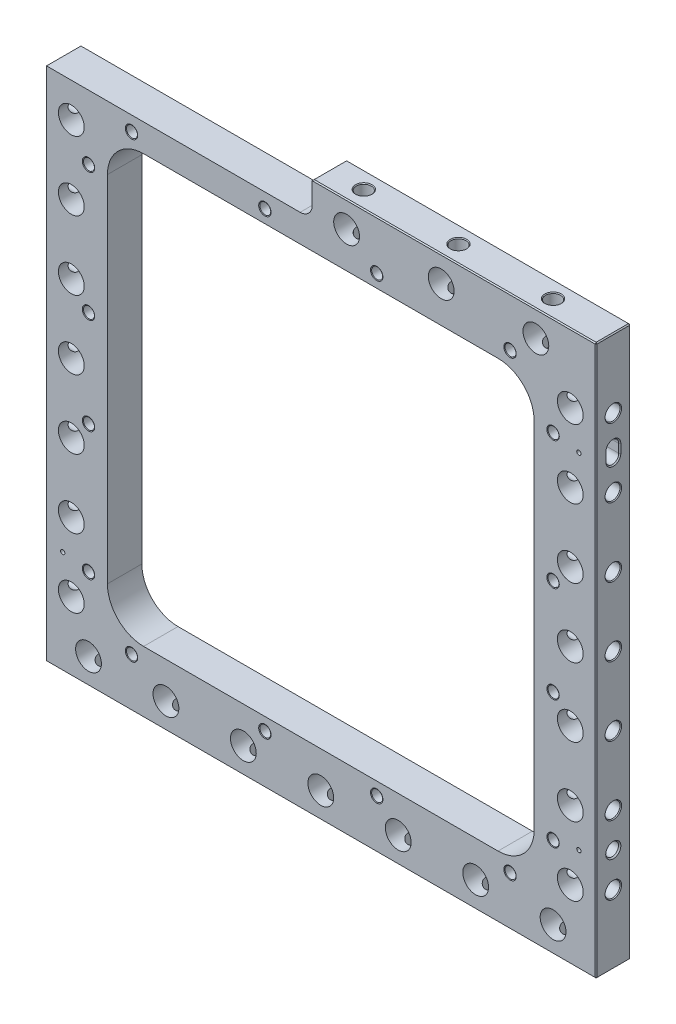
SolidWorks part; units mm, degrees
material "6061-T6 Al"
ref_plane "Front Plane" through (0, 0, 0) normal (0, 0, 1) x (1, 0, 0)
ref_plane "Top Plane" through (0, 0, 0) normal (0, 1, 0) x (1, 0, 0)
ref_plane "Right Plane" through (0, 0, 0) normal (1, 0, 0) x (0, 0, -1)
sketch "Sketch1" plane through (0, 0, 0) normal (0, 0, 1) x (1, 0, 0)
  line L0 (-203.2, 177.8) -> (-203.2, -203.2)
  line L1 (-203.2, -203.2) -> (203.2, -203.2)
  line L2 (203.2, -203.2) -> (203.2, 203.2)
  line L3 (203.2, 203.2) -> (-6.35, 203.2)
  line L4 (-6.35, 203.2) -> (-6.35, 177.8)
  line L5 (-6.35, 177.8) -> (-203.2, 177.8)
  line L6 (-203.2, -203.2) -> (203.2, 203.2) construction
  point P2 (0, 0)
  dimension "D1" = 406.4
  dimension "D2" = 209.55
  dimension "D3" = 406.4
  dimension "D4" = 25.4
extrude "Extrude1" add sketch "Sketch1" along normal mid plane 25.4
hole_wizard "3/4 (0.75) Diameter Hole1" positions "Sketch4" profile "Sketch3" hole size "3/4" standard "Ansi Inch" end condition through all
sketch "Sketch4" plane through (0, 0, 12.7) normal (0, 0, 1) x (1, 0, 0)
  line L0 (203.2, 0) -> (184.15, 0) construction
  line L1 (203.2, -203.2) -> (203.2, 203.2) construction
  line L5 (184.15, 0) -> (-184.15, 0) construction
  line L6 (-184.15, 0) -> (-203.2, 0) construction
  line L7 (-203.2, 177.8) -> (-203.2, -203.2) construction
  point P0 (184.15, 0)
  point P22 (-184.15, 0)
  dimension "D1" = 19.05
sketch "Sketch3" plane through (184.15, 0, 12.7) normal (1, 0, 0) x (0, -1, 0)
  line L0 (0, 0) -> (0, 25.4)
  line L1 (0, 25.4) -> (9.525, 25.4)
  line L2 (9.525, 25.4) -> (9.525, 0)
  line L5 (9.525, 0) -> (0, 0)
  line L11 (0, -6.35) -> (0, 107.95) construction
  dimension "Thru Hole Dia." = 19.05
  dimension "Thru Hole Depth" = 25.4
hole_wizard "7/16 (0.4375) Diameter Hole1" positions "Sketch6" profile "Sketch5" hole size "7/16" standard "Ansi Inch"
sketch "Sketch6" plane through (203.2, 0, 0) normal (1, 0, 0) x (0, 0, -1)
  line L0 (-12.7, 9.525) -> (-12.7, -9.525) construction
  line L1 (-12.7, 9.525) -> (-12.7, -9.525)
  line L2 (-12.7, 0) -> (0, 0) construction
  line L4 (0, 0) -> (12.7, 0) construction
  line L5 (12.7, -203.2) -> (12.7, 203.2) construction
  point P0 (0, 0)
sketch "Sketch5" plane through (203.2, 0, 0) normal (0, 1, 0) x (0, 0, -1)
  line L0 (0, 0) -> (0, 38.2635)
  line L1 (0, 38.2635) -> (5.5562, 34.925)
  line L2 (5.5562, 34.925) -> (5.5562, 0.6209)
  line L3 (5.5562, 0.6209) -> (6.096, 0)
  line L5 (6.096, 0) -> (0, 0)
  line L6 (-5.5562, 0.6209) -> (-6.096, 0) construction
  line L10 (0, 38.2635) -> (-5.5563, 34.925) construction
  line L11 (0, -6.35) -> (0, 107.95) construction
  dimension "Hole Dia." = 11.1125
  dimension "Hole Depth" = 34.925
  dimension "Near C'Sink Dia." = 12.192
  dimension "Near C'Sink Angle" = 82
  dimension "Drill Angle" = 118
hole_wizard "7/16 (0.4375) Diameter Hole2" positions "Sketch8" profile "Sketch7" hole size "7/16" standard "Ansi Inch"
sketch "Sketch8" plane through (-203.2, 0, 0) normal (-1, 0, 0) x (0, 0, 1)
  line L0 (12.7, -9.525) -> (12.7, 9.525) construction
  line L1 (12.7, -9.525) -> (12.7, 9.525)
  line L2 (12.7, 0) -> (0, 0) construction
  line L3 (0, 0) -> (-12.7, 0) construction
  line L4 (-12.7, 177.8) -> (-12.7, -203.2) construction
  point P0 (0, 0)
sketch "Sketch7" plane through (-203.2, 0, 0) normal (0, 1, 0) x (0, 0, 1)
  line L0 (0, 0) -> (0, 38.2635)
  line L1 (0, 38.2635) -> (5.5562, 34.925)
  line L2 (5.5562, 34.925) -> (5.5562, 0.6209)
  line L3 (5.5562, 0.6209) -> (6.096, 0)
  line L5 (6.096, 0) -> (0, 0)
  line L6 (-5.5562, 0.6209) -> (-6.096, 0) construction
  line L10 (0, 38.2635) -> (-5.5563, 34.925) construction
  line L11 (0, -6.35) -> (0, 107.95) construction
  dimension "Hole Dia." = 11.1125
  dimension "Hole Depth" = 34.925
  dimension "Near C'Sink Dia." = 12.192
  dimension "Near C'Sink Angle" = 82
  dimension "Drill Angle" = 118
pattern_linear "LPattern1" count 4 spacing 50.8 along (0, -1, 0) count 4 spacing 50.8 along (0, 1, 0) of "7/16 (0.4375) Diameter Hole2", "3/4 (0.75) Diameter Hole1", "7/16 (0.4375) Diameter Hole1"
hole_wizard "3/4 (0.75) Diameter Hole2" positions "Sketch10" profile "Sketch9" hole size "3/4" standard "Ansi Inch"
sketch "Sketch10" plane through (0, 0, 12.7) normal (0, 0, 1) x (1, 0, 0)
  line L0 (0, -184.15) -> (0, -203.2) construction
  line L1 (-203.2, -203.2) -> (203.2, -203.2) construction
  line L4 (0, -184.15) -> (0, 184.15) construction
  line L5 (0, 184.15) -> (0, 203.2) construction
  line L6 (203.2, 203.2) -> (-6.35, 203.2) construction
  point P1 (0, -184.15)
  dimension "D1" = 19.05
sketch "Sketch9" plane through (0, -184.15, 12.7) normal (1, 0, 0) x (0, -1, 0)
  line L0 (0, 0) -> (0, 40.6482)
  line L1 (0, 40.6482) -> (9.525, 34.925)
  line L2 (9.525, 34.925) -> (9.525, 0)
  line L5 (9.525, 0) -> (0, 0)
  line L10 (0, 40.6482) -> (-9.525, 34.925) construction
  line L11 (0, -6.35) -> (0, 107.95) construction
  dimension "Hole Dia." = 19.05
  dimension "Hole Depth" = 34.925
  dimension "Drill Angle" = 118
hole_wizard "7/16 (0.4375) Diameter Hole3" positions "Sketch12" profile "Sketch11" hole size "7/16" standard "Ansi Inch"
sketch "Sketch12" plane through (0, -203.2, 0) normal (0, -1, 0) x (1, 0, 0)
  line L0 (9.525, 12.7) -> (-9.525, 12.7) construction
  line L1 (9.525, 12.7) -> (-9.525, 12.7)
  line L2 (0, 12.7) -> (0, 0) construction
  line L5 (0, 0) -> (0, -12.7) construction
  line L6 (-203.2, -12.7) -> (203.2, -12.7) construction
  point P0 (0, 0)
sketch "Sketch11" plane through (0, -203.2, 0) normal (1, 0, 0) x (0, 0, -1)
  line L0 (0, 0) -> (0, 38.2635)
  line L1 (0, 38.2635) -> (5.5562, 34.925)
  line L2 (5.5562, 34.925) -> (5.5562, 0.6209)
  line L3 (5.5562, 0.6209) -> (6.096, 0)
  line L5 (6.096, 0) -> (0, 0)
  line L6 (-5.5562, 0.6209) -> (-6.096, 0) construction
  line L10 (0, 38.2635) -> (-5.5563, 34.925) construction
  line L11 (0, -6.35) -> (0, 107.95) construction
  dimension "Hole Dia." = 11.1125
  dimension "Hole Depth" = 34.925
  dimension "Near C'Sink Dia." = 12.192
  dimension "Near C'Sink Angle" = 82
  dimension "Drill Angle" = 118
hole_wizard "3/4 (0.75) Diameter Hole3" positions "Sketch16" profile "Sketch17" hole size "3/4" standard "Ansi Inch" end condition through all
sketch "Sketch16" plane through (0, 0, 12.7) normal (0, 0, 1) x (1, 0, 0)
  line L1 (19.05, 184.15) -> (19.05, 203.2) construction
  line L2 (203.2, 203.2) -> (-6.35, 203.2) construction
  line L4 (0, -184.15) -> (0, -203.2) construction
  line L5 (-203.2, -203.2) -> (203.2, -203.2) construction
  line L6 (-203.2, 177.8) -> (-203.2, -203.2) construction
  point P0 (19.05, 184.15)
  dimension "D1" = 222.25
sketch "Sketch17" plane through (19.05, 184.15, 12.7) normal (1, 0, 0) x (0, -1, 0)
  line L0 (0, 0) -> (0, 25.4)
  line L1 (0, 25.4) -> (9.525, 25.4)
  line L2 (9.525, 25.4) -> (9.525, 0)
  line L5 (9.525, 0) -> (0, 0)
  line L11 (0, -6.35) -> (0, 107.95) construction
  dimension "Thru Hole Dia." = 19.05
  dimension "Thru Hole Depth" = 25.4
hole_wizard "7/16 (0.4375) Diameter Hole4" positions "Sketch14" profile "Sketch13" hole size "7/16" standard "Ansi Inch"
sketch "Sketch14" plane through (0, 203.2, 0) normal (0, 1, 0) x (-1, 0, 0)
  line L2 (-19.05, 12.7) -> (-19.05, 0) construction
  line L3 (-19.05, 0) -> (-19.05, -12.7) construction
  line L4 (-203.2, -12.7) -> (6.35, -12.7) construction
  line L6 (-9.525, 12.7) -> (-28.575, 12.7) construction
  line L7 (-9.525, 12.7) -> (-28.575, 12.7)
  point P0 (-19.05, 0)
sketch "Sketch13" plane through (19.05, 203.2, 0) normal (1, 0, 0) x (0, 0, 1)
  line L0 (0, 0) -> (0, 38.2635)
  line L1 (0, 38.2635) -> (5.5562, 34.925)
  line L2 (5.5562, 34.925) -> (5.5562, 0.6209)
  line L3 (5.5562, 0.6209) -> (6.096, 0)
  line L5 (6.096, 0) -> (0, 0)
  line L6 (-5.5562, 0.6209) -> (-6.096, 0) construction
  line L10 (0, 38.2635) -> (-5.5563, 34.925) construction
  line L11 (0, -6.35) -> (0, 107.95) construction
  dimension "Hole Dia." = 11.1125
  dimension "Hole Depth" = 34.925
  dimension "Near C'Sink Dia." = 12.192
  dimension "Near C'Sink Angle" = 82
  dimension "Drill Angle" = 118
pattern_linear "LPattern2" count 4 spacing 57.15 along (-1, 0, 0) count 4 spacing 57.15 along (1, 0, 0) of "3/4 (0.75) Diameter Hole2", "7/16 (0.4375) Diameter Hole3"
pattern_linear "LPattern3" count 3 spacing 69.85 along (1, 0, 0) of "3/4 (0.75) Diameter Hole3", "7/16 (0.4375) Diameter Hole4"
sketch "Sketch18" plane through (0, 0, 12.7) normal (0, 0, 1) x (1, 0, 0)
  line L0 (157.48, 157.48) -> (-157.48, -157.48) construction
  line L1 (157.48, -157.48) -> (-157.48, -157.48)
  line L2 (157.48, -157.48) -> (157.48, 157.48)
  line L3 (157.48, 157.48) -> (-157.48, 157.48)
  line L4 (-157.48, -157.48) -> (-157.48, 157.48)
  line L5 (203.2, 203.2) -> (-6.35, 203.2) construction
  line L6 (-203.2, 177.8) -> (-203.2, -203.2) construction
  point P4 (0, 0)
  dimension "D1" = 45.72
  dimension "D2" = 45.72
extrude "Cut-Extrude1" cut sketch "Sketch18" against normal through all
fillet "Fillet1" radius 26.67 4 edges at (-157.48, 157.48, 0) (-157.48, -157.48, 0) (157.48, -157.48, 0) (157.48, 157.48, 0)
fillet "Fillet2" radius 8.89 1 edges at (-6.35, 177.8, 0)
hole_wizard "Tapped Hole for 1/4-20 Helicoil1" positions "Sketch20" profile "Sketch19" tap size "1/4-20" standard "Helicoil® Inch" end condition through all
sketch "Sketch20" plane through (0, 0, 12.7) normal (0, 0, 1) x (1, 0, 0)
  line L11 (-139.7, 167.005) -> (-41.275, 167.005) construction
  line L12 (-41.275, 167.005) -> (41.275, 167.005) construction
  line L13 (41.275, 167.005) -> (139.7, 167.005) construction
  line L16 (171.45, 130.175) -> (171.45, 35.56) construction
  line L17 (171.45, 35.56) -> (171.45, -35.56) construction
  line L20 (171.45, -35.56) -> (171.45, -130.175) construction
  line L23 (139.7, -167.005) -> (41.275, -167.005) construction
  line L24 (41.275, -167.005) -> (-41.275, -167.005) construction
  line L25 (-41.275, -167.005) -> (-139.7, -167.005) construction
  line L28 (0, 167.005) -> (0, 157.48) construction
  line L29 (130.81, 157.48) -> (-130.81, 157.48) construction
  line L33 (-171.45, 130.175) -> (-171.45, 35.56) construction
  line L34 (-171.45, 35.56) -> (-171.45, -35.56) construction
  line L35 (-171.45, -35.56) -> (-171.45, -130.175) construction
  line L38 (-171.45, 0) -> (-157.48, 0) construction
  line L39 (-157.48, 130.81) -> (-157.48, -130.81) construction
  line L42 (0, -167.005) -> (0, -157.48) construction
  line L43 (-130.81, -157.48) -> (130.81, -157.48) construction
  line L46 (171.45, 0) -> (157.48, 0) construction
  line L47 (157.48, -130.81) -> (157.48, 130.81) construction
  point P0 (-139.7, 167.005)
  point P96 (-41.275, 167.005)
  point P98 (41.275, 167.005)
  point P100 (139.7, 167.005)
  point P102 (-171.45, 130.175)
  point P104 (-171.45, 35.56)
  point P106 (-171.45, -35.56)
  point P108 (-171.45, -130.175)
  point P110 (-139.7, -167.005)
  point P112 (-41.275, -167.005)
  point P114 (41.275, -167.005)
  point P116 (139.7, -167.005)
  point P118 (171.45, -130.175)
  point P120 (171.45, -35.56)
  point P122 (171.45, 35.56)
  point P124 (171.45, 130.175)
  dimension "D1" = 342.9
  dimension "D2" = 279.4
  dimension "D3" = 260.35
  dimension "D4" = 82.55
  dimension "D5" = 71.12
  dimension "D6" = 334.01
sketch "Sketch19" plane through (-139.7, 167.005, 12.7) normal (1, 0, 0) x (0, -1, 0)
  line L0 (0, 0) -> (0, 25.4)
  line L1 (0, 25.4) -> (3.3782, 25.4)
  line L3 (3.3782, 25.4) -> (3.3782, 15.7226)
  line L4 (4.0475, 15.7226) -> (3.3782, 15.7226)
  line L5 (4.0475, 15.7226) -> (4.0475, 0.3028)
  line L6 (4.0475, 0.3028) -> (4.572, 0)
  line L7 (4.572, 0) -> (0, 0)
  line L8 (-4.0475, 0.3028) -> (-4.572, 0) construction
  line L11 (0, -6.35) -> (0, 107.95) construction
  dimension "Thru Tap Drill Dia." = 6.7564
  dimension "Thru Tap Drill Depth" = 25.4
  dimension "Thread Major Dia." = 8.095
  dimension "Thread Depth" = 15.7226
  dimension "Near C'Sink Dia." = 9.144
  dimension "Near C'Sink Angle" = 120
hole_wizard "3/8 (0.376) Pin Locate1" positions "Sketch24" profile "Sketch23" hole size "3/8" standard "Ansi Inch"
sketch "Sketch24" plane through (203.2, 0, 0) normal (1, 0, 0) x (0, 0, -1)
  line L0 (0, 0) -> (0, -127) construction
  point P0 (0, -127)
  dimension "D1" = 127
sketch "Sketch23" plane through (203.2, -127, 0) normal (0, 1, 0) x (0, 0, -1)
  line L0 (0, 0) -> (0, 18.1092)
  line L1 (0, 18.1092) -> (4.7752, 15.24)
  line L2 (4.7752, 15.24) -> (4.7752, 0.935)
  line L3 (4.7752, 0.935) -> (5.588, 0)
  line L5 (5.588, 0) -> (0, 0)
  line L6 (-4.7752, 0.935) -> (-5.588, 0) construction
  line L10 (0, 18.1092) -> (-4.7752, 15.24) construction
  line L11 (0, -6.35) -> (0, 107.95) construction
  dimension "Hole Dia." = 9.5504
  dimension "Hole Depth" = 15.24
  dimension "Near C'Sink Dia." = 11.176
  dimension "Near C'Sink Angle" = 82
  dimension "Drill Angle" = 118
sketch "Sketch27" plane through (203.2, 0, 0) normal (1, 0, 0) x (0, 0, -1)
  line L0 (0, 123.825) -> (0, 130.175) construction
  line L1 (4.7752, 123.825) -> (4.7752, 130.175)
  line L2 (-4.7752, 123.825) -> (-4.7752, 130.175)
  line L3 (0, 127) -> (0, 0) construction
  line L4 (0, 0) -> (0, -127) construction
  arc A0 (4.7752, 123.825) -> (-4.7752, 123.825) centre (0, 123.825) cw
  arc A1 (4.7752, 130.175) -> (-4.7752, 130.175) centre (0, 130.175) ccw
  dimension "D1" = 6.35
  dimension "D3" = 9.5504
  dimension "D2" = 4.7752
extrude "Cut-Extrude2" cut sketch "Sketch27" against normal blind 15.24
chamfer "Chamfer1" distance 0.762 angle 45 4 edges at (203.2, 134.9502, 0) (203.2, 127, 4.7752) (203.2, 127, -4.7752) (203.2, 119.0498, 0)
mirror "Mirror1" about plane through (0, 0, 0) normal (1, 0, 0) of "3/8 (0.376) Pin Locate1"
hole_wizard "1/8 (0.125) Diameter Hole1" positions "Sketch26" profile "Sketch25" hole size "1/8" standard "Ansi Inch"
sketch "Sketch26" plane through (1.9421, 0.0076, 12.7) normal (0, 0, -1) x (-1, 0, 0)
  line L0 (-186.0179, -122.2324) -> (-186.0179, -131.7828) construction
  line L1 (-186.0179, -122.2324) -> (-186.0179, -131.7828)
  line L2 (-186.0179, -127.0076) -> (-188.5579, -127.0076) construction
  line L3 (192.4421, -127.0076) -> (205.1421, -127.0076) construction
  line L4 (205.1421, 177.7924) -> (205.1421, -203.2076) construction
  line L7 (-188.5579, -127.0076) -> (-201.2579, -127.0076) construction
  line L8 (-201.2579, -203.2076) -> (-201.2579, 203.1924) construction
  point P0 (-188.5579, -127.0076)
  point P6 (-188.5579, 126.9924)
  point P8 (192.4421, -127.0076)
  dimension "D1" = 2.54
sketch "Sketch25" plane through (190.5, -127, 12.7) normal (1, 0, 0) x (0, -1, 0)
  line L0 (0, 0) -> (0, 10.6059)
  line L1 (0, 10.6059) -> (1.5875, 9.652)
  line L2 (1.5875, 9.652) -> (1.5875, 0)
  line L5 (1.5875, 0) -> (0, 0)
  line L10 (0, 10.6059) -> (-1.5875, 9.652) construction
  line L11 (0, -6.35) -> (0, 107.95) construction
  dimension "Hole Dia." = 3.175
  dimension "Hole Depth" = 9.652
  dimension "Drill Angle" = 118
chamfer "Chamfer2" distance 0.762 angle 45 13 edges at (-203.2, 177.8, 0) (-203.2, -12.7, 12.7) (-203.2, -12.7, -12.7) (-203.2, -203.2, 0) (0, -203.2, 12.7) (0, -203.2, -12.7) (203.2, -203.2, 0) (203.2, 0, -12.7) (203.2, 0, 12.7) (203.2, 203.2, 0) (98.425, 203.2, -12.7) (-6.35, 203.2, 0) (98.425, 203.2, 12.7)
